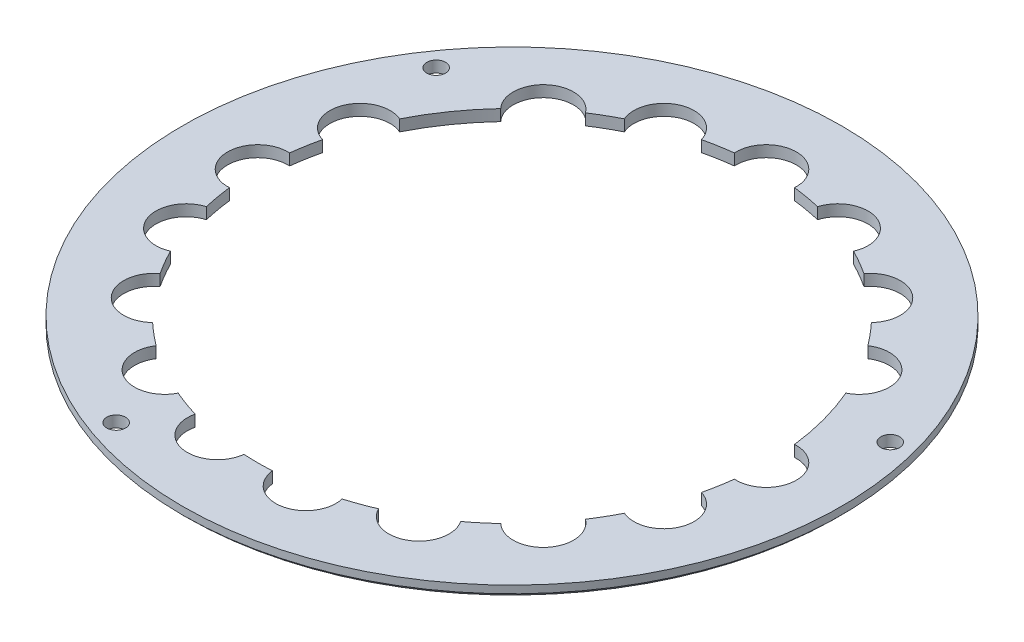
SolidWorks part; units mm, degrees
ref_plane "Front Plane" through (0, 0, 0) normal (0, 0, 1) x (1, 0, 0)
ref_plane "Top Plane" through (0, 0, 0) normal (0, 1, 0) x (1, 0, 0)
ref_plane "Right Plane" through (0, 0, 0) normal (1, 0, 0) x (0, 0, -1)
sketch "Sketch1" plane through (0, 0, 0) normal (0, 1, 0) x (1, 0, 0)
  circle A0 centre (0, 0) radius 17.5
  dimension "D1" = 35
extrude "Boss-Extrude1" add sketch "Sketch1" along normal blind 0.6
sketch "Sketch2" plane through (0, 0.6, 0) normal (0, 1, 0) x (1, 0, 0)
  circle A0 centre (0, 0) radius 13.5
  dimension "D1" = 27
extrude "Cut-Extrude1" cut sketch "Sketch2" against normal up to next
sketch "Sketch3" plane through (0, 0.6, 0) normal (0, 1, 0) x (1, 0, 0)
  line L0 (0, 0) -> (13.077, 7.55) construction
  line L1 (0, 0) -> (15.1, 0) construction
  circle A0 centre (0, 0) radius 15.1 construction
  circle A1 centre (11.6913, 6.75) radius 1.6
  dimension "D1" = 30.2
  dimension "D2" = 3.2
  dimension "D3" = 30
extrude "Cut-Extrude2" cut sketch "Sketch3" against normal up to next (0.6 mm away)
pattern_circular "CirPattern1" count 6 every 20 about axis through (0, 0, 0) along (0, 1, 0) of "Cut-Extrude2"
sketch "Sketch4" plane through (0, 0.6, 0) normal (0, 1, 0) x (1, 0, 0)
  circle A0 centre (13.5, 0) radius 1.6
  arc A1 (-9.8402, 9.2423) -> (12.4078, 5.3194) centre (0, 0) ccw construction
  arc A2 (12.4078, 5.3194) -> (10.8106, 8.0858) centre (11.6913, 6.75) ccw construction
extrude "Cut-Extrude3" cut sketch "Sketch4" against normal up to next (0.6 mm away)
pattern_circular "CirPattern2" count 11 every 20 about axis through (0, 0, 0) along (0, 1, 0) of "Cut-Extrude3"
hole_wizard "Ø1.0 (1) Diameter Hole1" positions "Sketch6" profile "Sketch5" hole size "Ø1.0" standard "DIN" end condition up to next
sketch "Sketch6" plane through (0, 0.6, 0) normal (0, 1, 0) x (1, 0, 0)
  line L0 (0, 0) -> (16.4, 0) construction
  line L1 (0, 0) -> (15.8412, 4.2446) construction
  line L2 (0, 0) -> (-5.6091, -15.411) construction
  line L4 (0, 0) -> (-13.4341, 9.4067) construction
  circle A0 centre (0, 0) radius 16.4 construction
  point P7 (15.8412, 4.2446)
  point P40 (-13.4341, 9.4067)
  point P44 (-5.6091, -15.411)
  dimension "D1" = 32.8
  dimension "D2" = 15
  dimension "D4" = 125
  dimension "D3" = 230
sketch "Sketch5" plane through (15.8412, 0.6, -4.2446) normal (1, 0, 0) x (0, 0, 1)
  line L0 (0, 0) -> (0, 0.6)
  line L1 (0, 0.6) -> (0.5, 0.6)
  line L2 (0.5, 0.6) -> (0.5, 0)
  line L5 (0.5, 0) -> (0, 0)
  line L11 (0, -6.35) -> (0, 107.95) construction
  dimension "Thru Hole Dia." = 1
  dimension "Thru Hole Depth" = 0.6
chamfer "Chamfer1" distance 0.2 angle 45 1 edges at (0, 0, 17.5)
